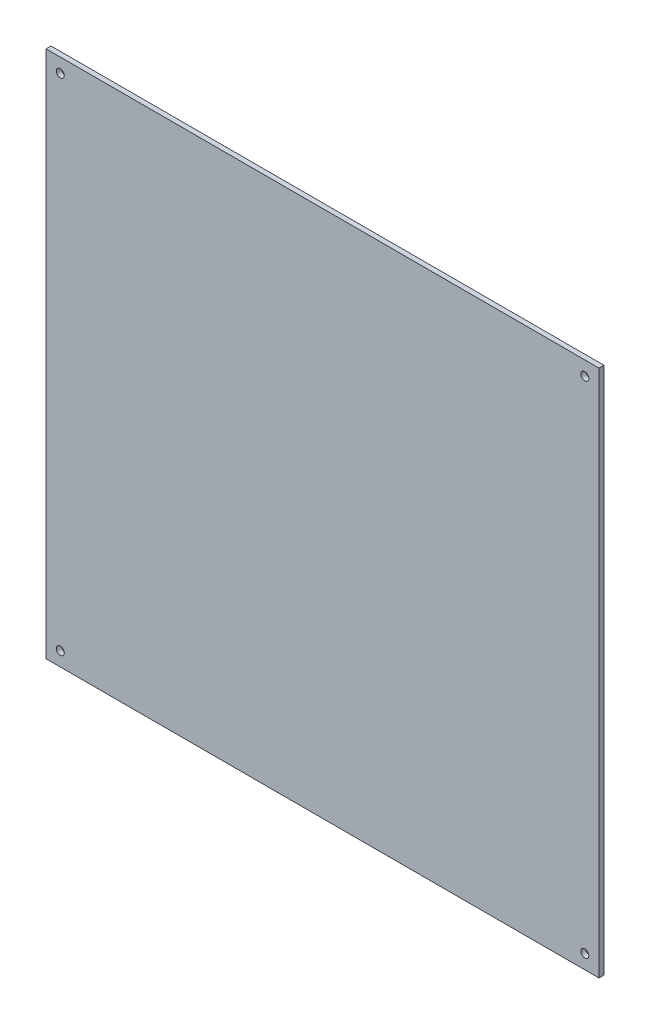
SolidWorks part; units mm, degrees
material "ABS PC"
ref_plane "Piano frontale" through (0, 0, 0) normal (0, 0, 1) x (1, 0, 0)
ref_plane "Piano superiore" through (0, 0, 0) normal (0, 1, 0) x (1, 0, 0)
ref_plane "Piano destro" through (0, 0, 0) normal (1, 0, 0) x (0, 0, -1)
sketch "Schizzo1" plane through (0, 0, 0) normal (0, 0, 1) x (1, 0, 0)
  line L0 (-224.5, 429) -> (-224.5, 0) construction
  line L1 (0, 0) -> (-449, 0)
  line L2 (0, 0) -> (0, 429)
  line L3 (0, 429) -> (-449, 429)
  line L4 (-449, 0) -> (-449, 429)
  line L5 (-449, 214.5) -> (0, 214.5) construction
  circle A0 centre (-437.5, 417.5) radius 3.25
  circle A1 centre (-11.5, 417.5) radius 3.25
  circle A2 centre (-437.5, 11.5) radius 3.25
  circle A3 centre (-11.5, 11.5) radius 3.25
  point P9 (-224.5, 214.5)
  dimension "D3" = 11.5
  dimension "D2" = 6.5
  dimension "D1" = 449
  dimension "314" = 429
  dimension "D4" = 11.5
extrude "Estrusione-Estrusione1" add sketch "Schizzo1" along normal blind 4
